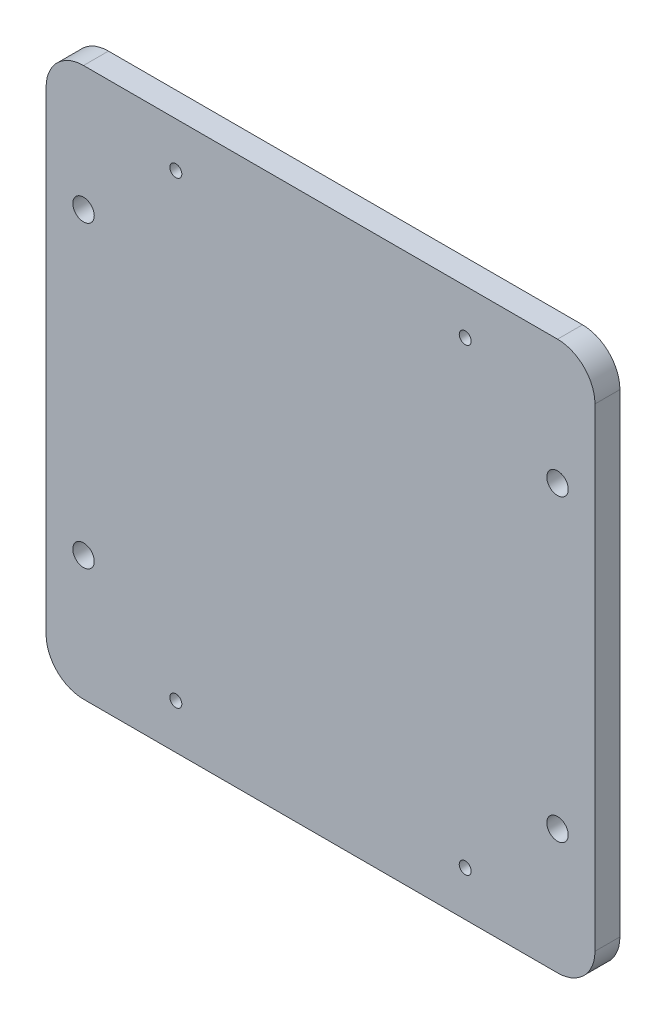
SolidWorks part; units mm, degrees
material "ﾎﾟﾘｳﾚﾀﾝ(POLYURETHANE) (11671)"
ref_plane "正面" through (0, 0, 0) normal (1, 0, 0) x (0, 1, 0)
ref_plane "平面" through (0, 0, 0) normal (0, 0, 1) x (0, 1, 0)
ref_plane "右側面" through (0, 0, 0) normal (0, 1, 0) x (-1, 0, 0)
sketch "ｽｹｯﾁ1" plane through (0, 0, 0) normal (0, 0, 1) x (0, 1, 0)
  line L1 (0, 0) -> (110, 0)
  line L2 (0, 0) -> (0, 110)
  line L3 (0, 110) -> (110, 110)
  line L4 (110, 0) -> (110, 110)
  line L5 (0, 0) -> (110, 110) construction
  line L6 (0, 110) -> (110, 0) construction
  point P4 (55, 55)
  dimension "D1" = 110
  dimension "D2" = 110
extrude "ﾎﾞｽ - 押し出し1" add sketch "ｽｹｯﾁ1" along normal blind 5
sketch "ｽｹｯﾁ2" plane through (0, 0, 5) normal (0, 0, 1) x (1, 0, 0)
  line L0 (0, 110) -> (-110, 110) construction
  line L1 (-84, 101) -> (-26, 101) construction
  line L2 (-84, 101) -> (-84, 9) construction
  line L3 (-84, 9) -> (-26, 9) construction
  line L4 (-26, 101) -> (-26, 9) construction
  line L5 (-84, 101) -> (-26, 9) construction
  line L6 (-84, 9) -> (-26, 101) construction
  line L7 (-110, 110) -> (-110, 0) construction
  point P7 (-55, 110)
  point P8 (-55, 101)
  point P11 (-110, 55)
  point P12 (-84, 55)
  point P14 (-84, 101)
  point P15 (-26, 101)
  point P16 (-26, 9)
  point P17 (-84, 9)
  point P18 (0, 0)
  dimension "D1" = 92
  dimension "D2" = 58
hole_wizard "M2 すきま穴1" positions "ｽｹｯﾁ2" profile "ｽｹｯﾁ3" hole size "M2" standard "JIS" end condition through all
sketch "ｽｹｯﾁ3" plane through (-84, 9, 5) normal (1, 0, 0) x (0, -1, 0)
  line L0 (0, 0) -> (0, 5)
  line L1 (0, 5) -> (1.2, 5)
  line L2 (1.2, 5) -> (1.2, 0)
  line L5 (1.2, 0) -> (0, 0)
  line L11 (0, -6.35) -> (0, 107.95) construction
  dimension "通し穴の直径" = 2.4
  dimension "通し穴の深さ" = 5
sketch "ｽｹｯﾁ4" plane through (0, 0, 5) normal (0, 0, 1) x (1, 0, 0)
  line L0 (-55, 110) -> (-55, 0) construction
  line L1 (0, 110) -> (-110, 110) construction
  line L2 (-110, 0) -> (0, 0) construction
  line L3 (-110, 110) -> (-110, 0) construction
  point P0 (-102.5, 85)
  point P1 (-102.5, 25)
  point P10 (-110, 55)
  point P11 (-7.5, 25)
  point P12 (-7.5, 85)
  point P13 (0, 0)
  dimension "D1" = 60
  dimension "D2" = 30
  dimension "D3" = 7.5
hole_wizard "M4 すきま穴1" positions "ｽｹｯﾁ4" profile "ｽｹｯﾁ5" hole size "M4" standard "JIS" end condition through all
sketch "ｽｹｯﾁ5" plane through (-102.5, 85, 5) normal (1, 0, 0) x (0, -1, 0)
  line L0 (0, 0) -> (0, 5)
  line L1 (0, 5) -> (2.15, 5)
  line L2 (2.15, 5) -> (2.15, 0)
  line L5 (2.15, 0) -> (0, 0)
  line L11 (0, -6.35) -> (0, 107.95) construction
  dimension "通し穴の直径" = 4.3
  dimension "通し穴の深さ" = 5
fillet "ﾌｨﾚｯﾄ1" radius 7.5 4 edges at (0, 110, 2.5) (0, 0, 2.5) (-110, 110, 2.5) (-110, 0, 2.5)
